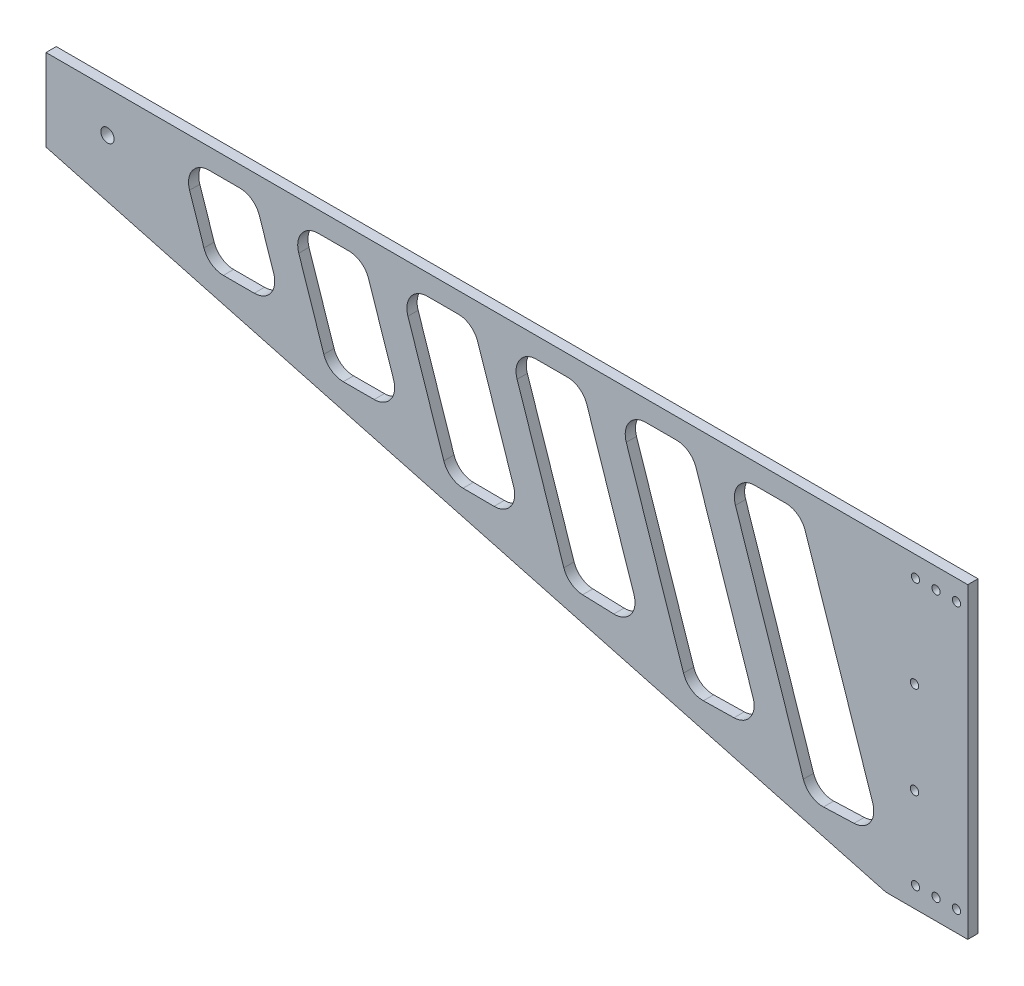
SolidWorks part; units mm, degrees
ref_plane "Ebene vorne" through (0, 0, 0) normal (0, 0, 1) x (1, 0, 0)
ref_plane "Ebene oben" through (0, 0, 0) normal (0, 1, 0) x (1, 0, 0)
ref_plane "Ebene rechts" through (0, 0, 0) normal (1, 0, 0) x (0, 0, -1)
sketch "Skizze1" plane through (0, 0, 0) normal (0, 0, 1) x (1, 0, 0)
  line L0 (0, 0) -> (0, -150)
  line L1 (-450, 0) -> (-450, -40)
  line L2 (-450, 0) -> (0, 0)
  line L3 (0, -150) -> (-40, -150)
  line L4 (-40, -150) -> (-450, -40)
  dimension "D1" = 450
  dimension "D2" = 150
  dimension "D3" = 40
  dimension "D4" = 40
extrude "Aufsatz-Linear austragen1" add sketch "Skizze1" along normal blind 5
sketch "Skizze2" plane through (0, 0, 5) normal (0, 0, 1) x (1, 0, 0)
  line L0 (0, -150) -> (0, 0) construction
  line L1 (0, 0) -> (-450, 0) construction
  circle A0 centre (-420, -20) radius 3.25
  point P18 (0, 0)
  dimension "D1" = 6.5
  dimension "D3" = 20
  dimension "D2" = 420
extrude "Schnitt-Linear austragen1" cut sketch "Skizze2" against normal through all
hole_wizard "Ø4.0 (4) Durchmesser Bohrung1" positions "Skizze3" profile "Skizze4" hole size "Ø4.0" standard "DIN" end condition through all
sketch "Skizze3" plane through (0, 0, 5) normal (0, 0, 1) x (1, 0, 0)
  point P0 (-25.5, -10)
  point P3 (-15.5, -10)
  point P6 (-5.5, -10)
  point P9 (-5.5, -140)
  point P12 (-15.5, -140)
  point P15 (-25.5, -140)
sketch "Skizze4" plane through (-25.5, -10, 5) normal (1, 0, 0) x (0, -1, 0)
  line L0 (0, 0) -> (0, 5)
  line L1 (0, 5) -> (2, 5)
  line L2 (2, 5) -> (2, 0)
  line L5 (2, 0) -> (0, 0)
  line L11 (0, -6.35) -> (0, 107.95) construction
  dimension "Bohrerdurchmesser" = 4
  dimension "Bohrungstiefe" = 5
hole_wizard "Ø4.1 (4.1) Durchmesser Bohrung1" positions "Skizze7" profile "Skizze8" hole size "Ø4.1" standard "DIN" end condition through all
sketch "Skizze7" plane through (0, 0, 0) normal (0, 0, -1) x (-1, 0, 0)
  point P0 (26, -55)
  point P3 (26, -100)
sketch "Skizze8" plane through (-26, -55, 0) normal (1, 0, 0) x (0, 1, 0)
  line L0 (0, 0) -> (0, 5)
  line L1 (0, 5) -> (2.05, 5)
  line L2 (2.05, 5) -> (2.05, 0)
  line L5 (2.05, 0) -> (0, 0)
  line L11 (0, -6.35) -> (0, 107.95) construction
  dimension "Bohrerdurchmesser" = 4.1
  dimension "Bohrungstiefe" = 5
sketch "Skizze9" plane through (0, 0, 5) normal (0, 0, 1) x (1, 0, 0)
  line L0 (-37.4087, -140.3416) -> (-523.2273, -10) construction
  line L3 (-450, -40) -> (-40, -150) construction
  line L4 (-391.6079, -10) -> (-60.7156, -10) construction
  line L5 (0, 0) -> (-450, 0) construction
  line L6 (-103.9316, -10) -> (-88.8473, -10)
  line L7 (-113.4162, -23.1689) -> (-104.1362, -50.9439)
  line L8 (-79.3627, -16.8311) -> (-67.9652, -50.9439)
  line L10 (-132.6591, -16.8311) -> (-121.2616, -50.9439)
  line L11 (-104.1362, -50.9439) -> (-80.2686, -122.3799)
  line L12 (-166.7126, -23.1689) -> (-157.4327, -50.9439)
  line L13 (-157.228, -10) -> (-142.1438, -10)
  line L14 (-185.9556, -16.8311) -> (-174.5581, -50.9439)
  line L15 (-67.9652, -50.9439) -> (-46.3979, -115.4949)
  line L16 (-220.009, -23.1689) -> (-210.7291, -50.9439)
  line L17 (-210.5244, -10) -> (-195.4402, -10)
  line L18 (-239.252, -16.8311) -> (-227.8545, -50.9439)
  line L19 (-70.417, -129.2043) -> (-55.5156, -128.6571)
  line L20 (-273.3055, -23.1689) -> (-264.0255, -50.9439)
  line L21 (-263.8208, -10) -> (-248.7366, -10)
  line L22 (-292.5484, -16.8311) -> (-281.1509, -50.9439)
  line L23 (-157.4327, -50.9439) -> (-138.7723, -106.7944)
  line L24 (-326.6019, -23.1689) -> (-317.3219, -50.9439)
  line L25 (-317.1173, -10) -> (-302.033, -10)
  line L26 (-345.8448, -16.8311) -> (-338.8472, -37.7749)
  line L27 (-121.2616, -50.9439) -> (-104.8199, -100.1541)
  line L28 (-379.8983, -23.1689) -> (-372.9007, -44.1128)
  line L29 (-370.4137, -10) -> (-355.3294, -10)
  line L35 (-129.0859, -113.6234) -> (-114.1027, -113.321)
  line L37 (-210.7291, -50.9439) -> (-197.1893, -91.4687)
  line L38 (-174.5581, -50.9439) -> (-162.9676, -85.6341)
  line L39 (-188.0345, -98.2943) -> (-172.782, -98.7976)
  line L41 (-264.0255, -50.9439) -> (-255.7943, -75.5799)
  line L42 (-227.8545, -50.9439) -> (-221.7035, -69.3537)
  line L43 (-246.3836, -82.4107) -> (-231.262, -82.5224)
  line L45 (-317.3219, -50.9439) -> (-314.3611, -59.8056)
  line L46 (-281.1509, -50.9439) -> (-280.3176, -53.4379)
  line L47 (-304.8568, -66.6366) -> (-289.7825, -66.6068)
  line L48 (-363.4161, -50.9439) -> (-348.3318, -50.9439)
  arc A0 (-314.3611, -59.8056) -> (-304.8568, -66.6366) centre (-304.8765, -56.6366) ccw
  arc A1 (-280.3176, -53.4379) -> (-289.7825, -66.6068) centre (-289.8022, -56.6068) cw
  arc A2 (-255.7943, -75.5799) -> (-246.3836, -82.4107) centre (-246.3097, -72.4109) ccw
  arc A3 (-221.7035, -69.3537) -> (-231.262, -82.5224) centre (-231.1881, -72.5226) cw
  arc A4 (-197.1893, -91.4687) -> (-188.0345, -98.2943) centre (-187.7046, -88.2997) ccw
  arc A5 (-162.9676, -85.6341) -> (-172.782, -98.7976) centre (-172.4522, -88.803) cw
  arc A6 (-138.7723, -106.7944) -> (-129.0859, -113.6234) centre (-129.2877, -103.6255) ccw
  arc A7 (-80.2686, -122.3799) -> (-70.417, -129.2043) centre (-70.784, -119.211) ccw
  arc A8 (-46.3979, -115.4949) -> (-55.5156, -128.6571) centre (-55.8825, -118.6638) cw
  arc A9 (-363.4161, -50.9439) -> (-372.9007, -44.1128) centre (-363.4161, -40.9439) cw
  arc A10 (-338.8472, -37.7749) -> (-348.3318, -50.9439) centre (-348.3318, -40.9439) cw
  arc A11 (-345.8448, -16.8311) -> (-355.3294, -10) centre (-355.3294, -20) ccw
  arc A12 (-379.8983, -23.1689) -> (-370.4137, -10) centre (-370.4137, -20) cw
  arc A13 (-292.5484, -16.8311) -> (-302.033, -10) centre (-302.033, -20) ccw
  arc A14 (-326.6019, -23.1689) -> (-317.1173, -10) centre (-317.1173, -20) cw
  arc A15 (-239.252, -16.8311) -> (-248.7366, -10) centre (-248.7366, -20) ccw
  arc A16 (-273.3055, -23.1689) -> (-263.8208, -10) centre (-263.8208, -20) cw
  arc A17 (-185.9556, -16.8311) -> (-195.4402, -10) centre (-195.4402, -20) ccw
  arc A18 (-220.009, -23.1689) -> (-210.5244, -10) centre (-210.5244, -20) cw
  arc A19 (-132.6591, -16.8311) -> (-142.1438, -10) centre (-142.1438, -20) ccw
  arc A20 (-104.8199, -100.1541) -> (-114.1027, -113.321) centre (-114.3045, -103.323) cw
  arc A21 (-88.8473, -10) -> (-79.3627, -16.8311) centre (-88.8473, -20) cw
  arc A22 (-113.4162, -23.1689) -> (-103.9316, -10) centre (-103.9316, -20) cw
  arc A23 (-166.7126, -23.1689) -> (-157.228, -10) centre (-157.228, -20) cw
  point P54 (-312.074, -66.6509)
  point P59 (-253.5297, -82.3579)
  point P64 (-194.9854, -98.0649)
  point P69 (-136.441, -113.7719)
  point P72 (-77.8967, -129.4789)
  point P77 (-370.6184, -50.9439)
  point P102 (-81.6451, -10)
  point P105 (-117.8161, -10)
  dimension "D14" = 10
  dimension "D1" = 10
  dimension "D2" = 10
  dimension "D4" = 180
  dimension "D5" = 180
  dimension "D6" = 180
  dimension "D7" = 180
  dimension "D8" = 180
  dimension "D9" = 10
  dimension "D10" = 10
  dimension "D11" = 10
  dimension "D12" = 10
  dimension "D13" = 10
  dimension "D3" = 6
extrude "Schnitt-Linear austragen2" cut sketch "Skizze9" against normal blind 8
